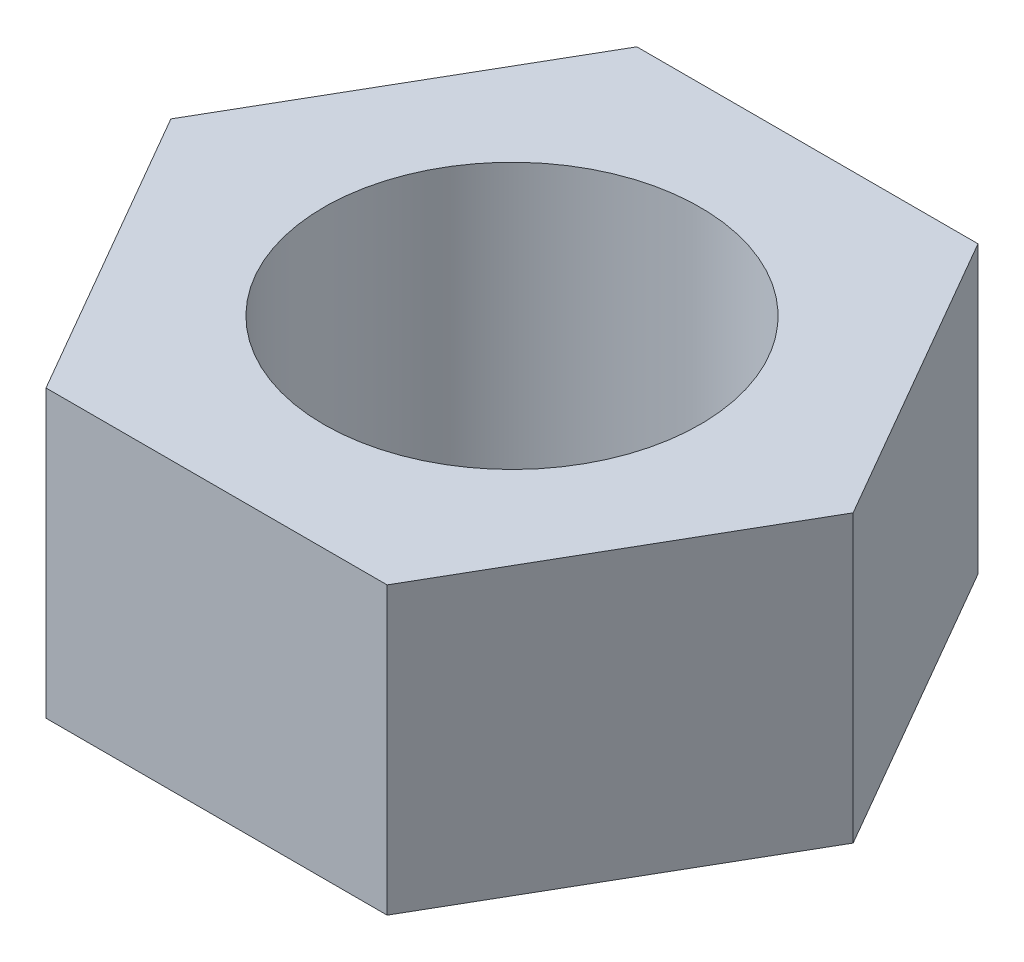
SolidWorks part; units mm, degrees
ref_plane "前视基准面" through (0, 0, 0) normal (0, 0, 1) x (1, 0, 0)
ref_plane "上视基准面" through (0, 0, 0) normal (0, 1, 0) x (1, 0, 0)
ref_plane "右视基准面" through (0, 0, 0) normal (1, 0, 0) x (0, 0, -1)
sketch "草图1" plane through (0, 0, 0) normal (0, 1, 0) x (1, 0, 0)
  line L7 (4.5322, 0) -> (2.2661, 3.925)
  line L8 (2.2661, 3.925) -> (-2.2661, 3.925)
  line L9 (-2.2661, 3.925) -> (-4.5322, 0)
  line L10 (-4.5322, 0) -> (-2.2661, -3.925)
  line L11 (-2.2661, -3.925) -> (2.2661, -3.925)
  line L12 (2.2661, -3.925) -> (4.5322, 0)
  circle A0 centre (0, 0) radius 3.925 construction
  circle A1 centre (0, 0) radius 2.5
extrude "凸台-拉伸1" add sketch "草图1" along normal blind 3.8
